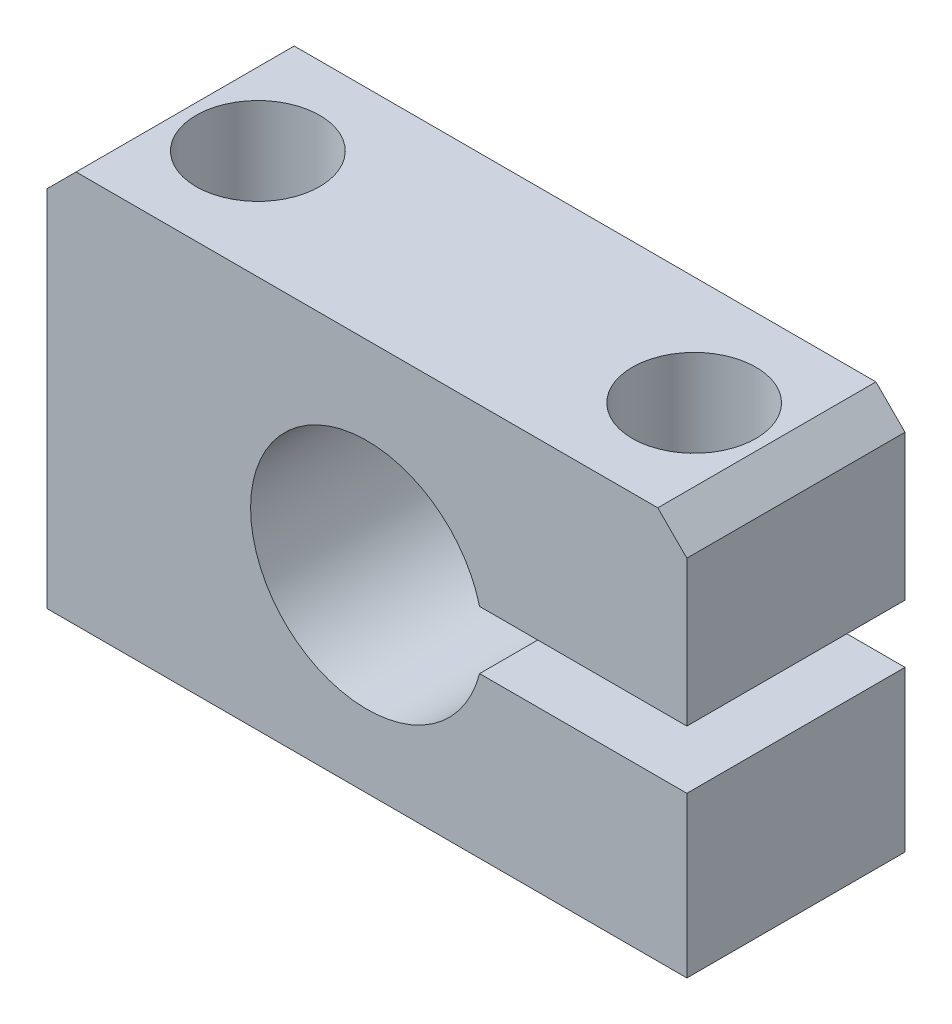
SolidWorks part; units mm, degrees
ref_plane "Front Plane" through (0, 0, 0) normal (0, 0, 1) x (1, 0, 0)
ref_plane "Top Plane" through (0, 0, 0) normal (0, 1, 0) x (1, 0, 0)
ref_plane "Right Plane" through (0, 0, 0) normal (1, 0, 0) x (0, 0, -1)
sketch "Sketch1" plane through (0, 0, 0) normal (0, 0, 1) x (1, 0, 0)
  line L0 (0, 0) -> (0, 30.6965) construction
  line L1 (22, 0) -> (-22, 0)
  line L2 (-22, 0) -> (-22, 27)
  line L3 (-22, 27) -> (22, 27)
  line L4 (22, 0) -> (22, 27)
  circle A0 centre (0, 13) radius 8
  point P10 (0, 27)
  dimension "D3" = 16
  dimension "D1" = 27
  dimension "D2" = 22
  dimension "D4" = 13
extrude "Boss-Extrude1" add sketch "Sketch1" along normal blind 15
sketch "Sketch2" plane through (0, 27, 0) normal (0, 1, 0) x (1, 0, 0)
  line L0 (0, 0) -> (0, -15) construction
  line L1 (22, -15) -> (-22, -15) construction
  line L2 (-22, -7.5) -> (22, -7.5) construction
  line L3 (-22, -15) -> (-22, 0) construction
  line L4 (22, -15) -> (22, 0) construction
  circle A0 centre (-15, -7.5) radius 3.2711
  circle A1 centre (15, -7.5) radius 3.2711
  dimension "D1" = 15
hole_wizard "CBORE for M5 Hex Socket Head Cap Screw1" positions "3DSketch1" profile "Sketch3" counterbore size "M5" standard "ISO" end condition up to next
sketch3d "3DSketch1"
  point P0 (-15, 27, 7.5)
  point P3 (15, 27, 7.5)
sketch "Sketch3" plane through (-15, 27, 7.5) normal (1, 0, 0) x (0, 0, 1)
  line L0 (0, 0) -> (0, 27)
  line L1 (0, 27) -> (2.75, 27)
  line L3 (2.75, 27) -> (2.75, 6)
  line L4 (2.75, 6) -> (4.25, 6)
  line L5 (4.25, 6) -> (4.25, 0)
  line L7 (4.25, 0) -> (0, 0)
  line L11 (0, -6.35) -> (0, 107.95) construction
  dimension "Thru Hole Dia." = 5.5
  dimension "Thru Hole Depth" = 27
  dimension "C'Bore Dia." = 8.5
  dimension "C'Bore Depth" = 6
chamfer "Chamfer1" distance 2 angle 45 2 edges at (-22, 27, 7.5) (22, 27, 7.5)
sketch "Sketch4" plane through (0, 0, 15) normal (0, 0, 1) x (1, 0, 0)
  line L0 (0, 13) -> (25.8666, 13) construction
  line L1 (7.746, 15) -> (22, 15)
  line L2 (22, 0) -> (22, 25) construction
  line L3 (22, 15) -> (22, 11)
  line L4 (7.746, 11) -> (22, 11)
  circle A0 centre (0, 13) radius 8 construction
  arc A1 (7.746, 11) -> (7.746, 15) centre (0, 13) ccw
  dimension "D1" = 2
extrude "Cut-Extrude1" cut sketch "Sketch4" against normal up to next
